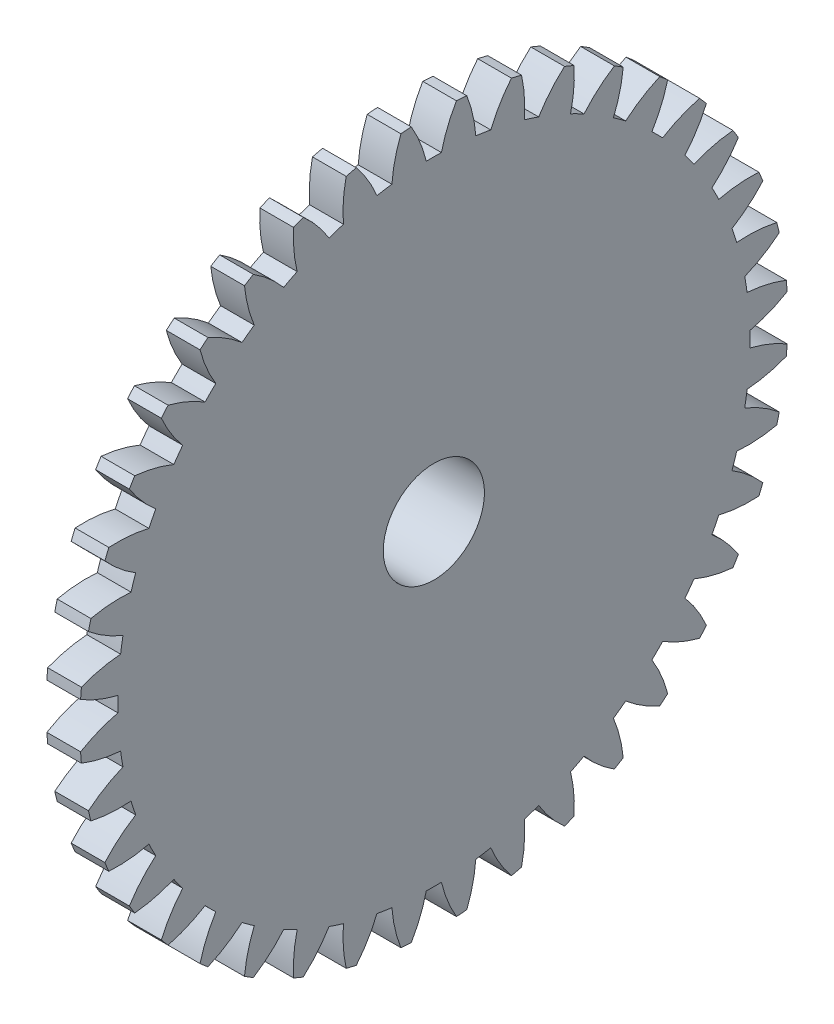
SolidWorks part; units mm, degrees
ref_plane "Plane1" through (0, 0, 0) normal (0, 0, 1) x (1, 0, 0)
ref_plane "Plane2" through (0, 0, 0) normal (0, 1, 0) x (1, 0, 0)
ref_plane "Plane3" through (0, 0, 0) normal (1, 0, 0) x (0, 0, -1)
sketch "HoldingSke" plane through (0, 0, 0) normal (0, 1, 0) x (1, 0, 0)
  line L0 (0, 0) -> (0.766, -0.6428)
  line L1 (-15, 0) -> (100, 0) construction
  line L2 (0, 0) -> (-2.1039, 2.3779)
  line L3 (0, 0) -> (-11.863, 4.5341)
  line L4 (0, 0) -> (6.6156, 5.5511)
  line L5 (0, 0) -> (-5.6217, -2.0967)
  line L6 (0, 0) -> (-1.6579, -1.1186)
  line L7 (-2.1039, 2.3779) -> (-0.8124, 8.2373)
  line L8 (-76.2, 54.61) -> (-75.2, 54.61)
  line L9 (-71.009, 38.7566) -> (-53.1078, 45.2721)
  line L10 (-76.2, 71.12) -> (104.1128, 71.12)
  line L11 (0, 0) -> (-2, 0)
  line L12 (-76.2, 101.6) -> (-76.162, 101.6)
  line L13 (24.9733, 27.94) -> (52.9518, 28.4284)
  line L14 (24.9733, 27.94) -> (24.9743, 27.94)
  line L15 (24.9733, 27.94) -> (100.4006, 29.5858)
  line L16 (-63.627, -1) -> (-12.827, -1)
  circle A0 centre (0, 0) radius 3
  circle A1 centre (0, 0) radius 9
  circle A2 centre (0, 0) radius 9
  circle A3 centre (0, 0) radius 3
  dimension "MHD" = 18
  dimension "Hub_dia" = 18
  dimension "Bore" = 6
  dimension "MBD" = 6
  dimension "Num_teeth" = 40
  dimension "Pitch_radius" = 180.3128
  dimension "Pitch" = 1
  dimension "Width" = 2
  dimension "Overall_len" = 6
  dimension "Show_teeth" = 40
  dimension "Thickness" = 2
  dimension "OAL" = 6.0001
  dimension "T_dim" = 1
  dimension "Ap" = 20
  dimension "H" = 19.05
  dimension "Backlash" = 0.038
  dimension "Addendum_fac" = 1
  dimension "Dedendum_fac" = 1.25
  dimension "Clearance_fac" = 0.25
  dimension "Dedendum_add" = 0.001
  dimension "Module" = 1
sketch "BasProSke" plane through (0, 0, 0) normal (0, 1, 0) x (1, 0, 0)
  line L0 (-10, 0) -> (60, 0) construction
  line L1 (0, 0) -> (0, 21)
  line L2 (0, 0) -> (2, 0)
  line L3 (2, 0) -> (2, 21)
  line L4 (2, 21) -> (0, 21)
  dimension "Diameter" = 42
  dimension "Thickness" = 2
revolve "Base-Revolve" add sketch "BasProSke" angle 360 about L0
sketch "TooCutSke" plane through (0, 0, 0) normal (1, 0, 0) x (0, 0, -1)
  line L1 (0, 0) -> (0, 107) construction
  line L2 (0, 0) -> (-0.8517, 19.9819) construction
  line L3 (0, 0) -> (-3.1363, 39.8509) construction
  line L4 (-0.8517, 19.9819) -> (-1.5682, 19.9255) construction
  arc A0 (0.4487, 18.7436) -> (-0.4487, 18.7436) centre (0, 0) ccw
  arc A1 (1.3547, 20.9817) -> (-1.3547, 20.9817) centre (0, 0) ccw
  circle A2 centre (0, 0) radius 20 construction
  circle A3 centre (0, 0) radius 18.7939 construction
  arc A4 (-0.4487, 18.7436) -> (-1.3547, 20.9817) centre (-8.2322, 16.895) ccw
  arc A5 (1.3547, 20.9817) -> (0.4487, 18.7436) centre (8.2322, 16.895) ccw
  dimension "Root_dia" = 37.498
  dimension "Overcut_dia" = 42.0508
  dimension "Pitch_dia" = 40
  dimension "Base_dia" = 37.5877
  dimension "Flank_rad" = 8
  dimension "Half_ang" = 4.5
  dimension "Half_CT" = 0.7187
extrude "ToothCut" cut sketch "TooCutSke" along normal through all
fillet "Breaks" [suppressed] radius 0.02
fillet "RootFillets" [suppressed] radius 0.251
pattern_circular "TeethCuts" count 40 every 9 about axis through (-10, 0, 0) along (1, 0, 0) of "ToothCut", "RootFillets", "Breaks"
sketch "HubNeaOneSke" plane through (0, 0, 0) normal (-1, 0, 0) x (0, 0, 1)
  circle A0 centre (0, 0) radius 9
  dimension "Diameter" = 18
extrude "HubNearOne" add sketch "HubNeaOneSke" along normal blind 4.0001
sketch "HubNeaBotSke" plane through (0, 0, 0) normal (-1, 0, 0) x (0, 0, 1)
  circle A0 centre (0, 0) radius 9
  dimension "Diameter" = 18
extrude "HubNearBoth" [suppressed] add sketch "HubNeaBotSke" along normal blind 2
ref_plane "FarPln" through (2, 0, 0) normal (1, 0, 0) x (0, 0, -1)
sketch "HubFarSke" plane through (2, 0, 0) normal (1, 0, 0) x (0, 0, -1)
  circle A0 centre (0, 0) radius 9
  dimension "Diameter" = 18
extrude "HubFar" [suppressed] add sketch "HubFarSke" along normal blind 2
sketch "BorSke" plane through (0, 0, 0) normal (1, 0, 0) x (0, 0, -1)
  circle A0 centre (0, 0) radius 3
  dimension "Diameter" = 6
extrude "Bore" cut sketch "BorSke" along normal mid plane 12.0001
sketch "KeySke" plane through (0, 0, 0) normal (1, 0, 0) x (0, 0, -1)
  line L0 (-1, 0) -> (-1, 4)
  line L1 (-1, 4) -> (1, 4)
  line L2 (1, 4) -> (1, 0)
  line L3 (0, 0) -> (0, 34) construction
  line L4 (-1, 0) -> (1, 0)
  dimension "Offset" = 4
  dimension "Width" = 2
extrude "Keyway" [suppressed] cut sketch "KeySke" along normal mid plane 12.0001
pattern_circular "Keyway2" [suppressed] count 2 every 90 about axis through (-10, 0, 0) along (1, 0, 0)
equation "' \"Module@HoldingSke\" = 6.35"
equation "' \"Num_teeth@HoldingSke\" = 12"
equation "' \"Ap@HoldingSke\" =  20"
equation "' \"Width@HoldingSke\" = 0.5 * 25.4"
equation "' \"Hub_dia@HoldingSke\"= 1 * 25.4"
equation "' \"Overall_len@HoldingSke\" = 1.0 * 25.4"
equation "' \"Bore@HoldingSke\" = 0.75 * 25.4"
equation "' \"T_dim@HoldingSke\" = 0.1 * 25.4"
equation "' \"Width@KeySke\" = 0.25 * 25.4"
equation "' \"Show_teeth@HoldingSke\" = 13"
equation "' \"Backlash@HoldingSke\" = 0.009 * 25.4"
equation "' \"Addendum_fac@HoldingSke\" = 1.0"
equation "' \"Dedendum_fac@HoldingSke\" = 1.25"
equation "' \"Dedendum_add@HoldingSke\" = 0.00005 * 25.4"
equation "' \"Clearance_fac@HoldingSke\" = 0.25"
equation "\"Pitch@HoldingSke\" = 1 / \"Module@HoldingSke\""
equation "\"Overcut_dia@TooCutSke\" = (\"Num_teeth@HoldingSke\" + 2 * \"Addendum_fac@HoldingSke\") / \"Pitch@HoldingSke\" + 0.002 * 25.4"
equation "\"Pitch_dia@TooCutSke\" = \"Num_teeth@HoldingSke\" / \"Pitch@HoldingSke\""
equation "\"Base_dia@TooCutSke\" = \"Num_teeth@HoldingSke\" / \"Pitch@HoldingSke\" * cos((\"Ap@HoldingSke\"  * 3.14159265 / 180))"
equation "\"Root_dia@TooCutSke\" = (\"Num_teeth@HoldingSke\" + 2) / \"Pitch@HoldingSke\" - 2 * (\"Addendum_fac@HoldingSke\" + \"Dedendum_fac@HoldingSke\") / \"Pitch@HoldingSke\" - \"Dedendum_add@HoldingSke\" * 2"
equation "\"Half_ang@TooCutSke\" = 180 / \"Num_teeth@HoldingSke\""
equation "\"Half_CT@TooCutSke\" = \"Num_teeth@HoldingSke\" / \"Pitch@HoldingSke\" * sin((3.14159265 / 2 / \"Num_teeth@HoldingSke\")) / 2 - 7 * \"Backlash@HoldingSke\" / 4"
equation "\"Flank_rad@TooCutSke\" = \"Num_teeth@HoldingSke\" / \"Pitch@HoldingSke\" / 5"
equation "\"Radius@RootFillets\" = \"Clearance_fac@HoldingSke\" / \"Pitch@HoldingSke\" + \"Dedendum_add@HoldingSke\""
equation "\"Break_rad@Breaks\" = 0.02 / \"Pitch@HoldingSke\""
equation "\"Thickness@HoldingSke\" = \"Width@HoldingSke\""
equation "\"OAL@HoldingSke\" = \"Thickness@HoldingSke\""
equation "\"MHD@HoldingSke\" = (\"Num_teeth@HoldingSke\" + 2) / \"Pitch@HoldingSke\" - 2 * (\"Addendum_fac@HoldingSke\" + \"Dedendum_fac@HoldingSke\")  / \"Pitch@HoldingSke\" - \"Dedendum_add@HoldingSke\" * 2"
equation "\"MBD@HoldingSke\" = (\"Num_teeth@HoldingSke\" + 2) / \"Pitch@HoldingSke\" - 2 * (\"Addendum_fac@HoldingSke\" + \"Dedendum_fac@HoldingSke\")  / \"Pitch@HoldingSke\" - \"Dedendum_add@HoldingSke\" * 2 - 0.002 * 25.4"
equation "\"MHD@HoldingSke\" = ((sgn( \"MHD@HoldingSke\" - \"Hub_dia@HoldingSke\" )-1)*( \"MHD@HoldingSke\" - \"Hub_dia@HoldingSke\" ))/-2+ \"Hub_dia@HoldingSke\""
equation "\"MBD@HoldingSke\" = ((sgn( \"MBD@HoldingSke\" - \"Bore@HoldingSke\" )-1)*( \"MBD@HoldingSke\" - \"Bore@HoldingSke\" ))/-2+ \"Bore@HoldingSke\""
equation "\"OAL@HoldingSke\" = ((sgn( \"OAL@HoldingSke\" - \"Overall_len@HoldingSke\" )+1)*( \"OAL@HoldingSke\" - \"Overall_len@HoldingSke\" ))/2 + \"Overall_len@HoldingSke\" + 0.000002 * 25.4"
equation "\"Num_teeth@TeethCuts\" = int( \"Show_teeth@HoldingSke\" ) + 1"
equation "\"Num_teeth@TeethCuts\" = ((sgn( \"Num_teeth@TeethCuts\" - \"Num_teeth@HoldingSke\" )-1)*( \"Num_teeth@TeethCuts\" - \"Num_teeth@HoldingSke\" ))/-2+ \"Num_teeth@HoldingSke\""
equation "\"Num_teeth@TeethCuts\" = ((sgn( \"Num_teeth@TeethCuts\" - 2.0)+1)*( \"Num_teeth@TeethCuts\" - 2.0))/2 +2.0"
equation "\"Angle@TeethCuts\" = 360.0 / \"Num_teeth@HoldingSke\""
equation "\"Diameter@BasProSke\" = (\"Num_teeth@HoldingSke\" + 2 * \"Addendum_fac@HoldingSke\") / \"Pitch@HoldingSke\""
equation "\"Thickness@BasProSke\"  = \"Thickness@HoldingSke\""
equation "' \"Fillet_rad@BasProSke\" =  \"Thickness@HoldingSke\" * 0.05"
equation "\"MHD@HoldingSke\" = ((sgn( \"MHD@HoldingSke\" - \"Root_dia@TooCutSke\" )-1)*( \"MHD@HoldingSke\" - \"Root_dia@TooCutSke\" ))/-2+ \"Root_dia@TooCutSke\""
equation "\"Diameter@HubNeaOneSke\" = \"MHD@HoldingSke\""
equation "\"Length@HubNearOne\" = \"OAL@HoldingSke\" - \"Thickness@BasProSke\""
equation "\"Diameter@HubNeaBotSke\" = \"MHD@HoldingSke\""
equation "\"Length@HubNearBoth\" = ( \"OAL@HoldingSke\" - \"Thickness@BasProSke\" ) / 2.0"
equation "\"Thickness@FarPln\" = \"Thickness@BasProSke\""
equation "\"Diameter@HubFarSke\" = \"MHD@HoldingSke\""
equation "\"Length@HubFar\" = ( \"OAL@HoldingSke\" - \"Thickness@BasProSke\" ) / 2.0"
equation "\"Diameter@BorSke\" = \"MBD@HoldingSke\""
equation "\"D1@Bore\" = \"OAL@HoldingSke\" * 2.0"
equation "\"D1@Keyway\" = \"OAL@HoldingSke\" * 2.0"
equation "\"Offset@KeySke\" = \"T_dim@HoldingSke\" + \"MBD@HoldingSke\" / 2.0"
